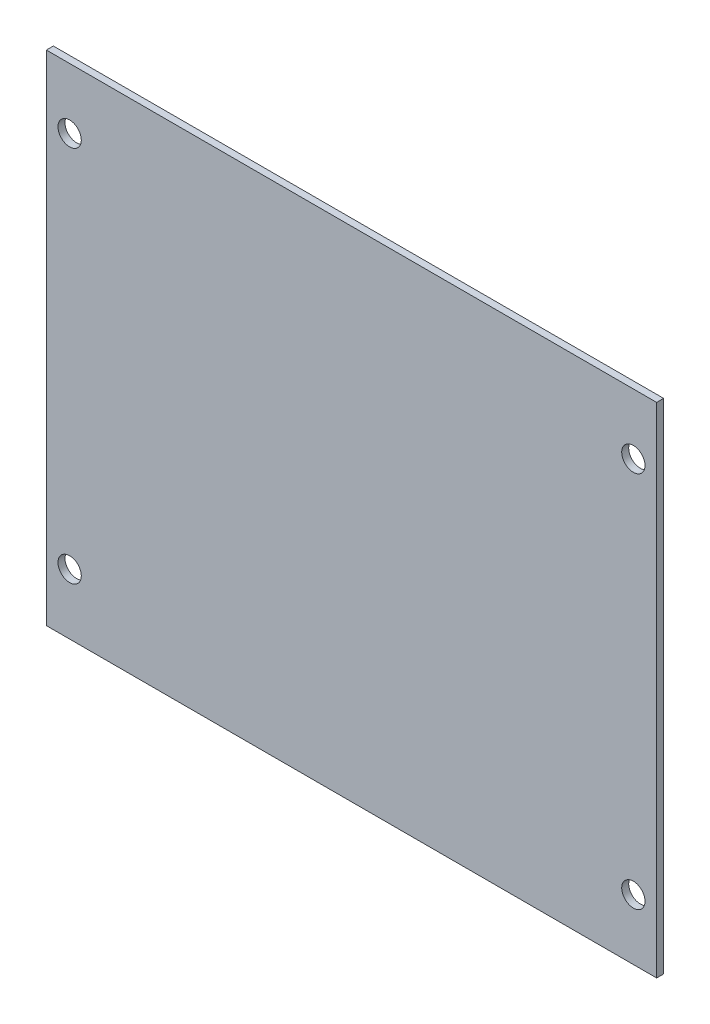
SolidWorks part; units mm, degrees
ref_plane "Alzado" through (0, 0, 0) normal (0, 0, 1) x (1, 0, 0)
ref_plane "Planta" through (0, 0, 0) normal (0, 1, 0) x (1, 0, 0)
ref_plane "Vista lateral" through (0, 0, 0) normal (1, 0, 0) x (0, 0, -1)
sketch "Croquis1" plane through (0, 0, 0) normal (0, 0, 1) x (1, 0, 0)
  line L1 (-55.0355, 36.5593) -> (75.9645, 36.5593)
  line L2 (-55.0355, 36.5593) -> (-55.0355, -70.4407)
  line L3 (-55.0355, -70.4407) -> (75.9645, -70.4407)
  line L4 (75.9645, 36.5593) -> (75.9645, -70.4407)
  dimension "D1" = 131
  dimension "D2" = 107
extrude "Saliente-Extruir1" add sketch "Croquis1" along normal blind 1.5
sketch "Croquis2" plane through (0, 0, 1.5) normal (0, 0, 1) x (1, 0, 0)
  line L0 (75.9645, -70.4407) -> (75.9645, 36.5593) construction
  line L1 (75.9645, 36.5593) -> (-55.0355, 36.5593) construction
  line L2 (-55.0355, 36.5593) -> (-55.0355, -70.4407) construction
  line L3 (-55.0355, -70.4407) -> (75.9645, -70.4407) construction
  circle A0 centre (-50.0355, 23.5593) radius 2.5
  circle A1 centre (70.9645, 23.5593) radius 2.5
  circle A2 centre (70.9645, -57.4407) radius 2.5
  circle A3 centre (-50.0355, -57.4407) radius 2.5
  dimension "D1" = 5
  dimension "D5" = 5
  dimension "D6" = 5
  dimension "D8" = 5
  dimension "D2" = 13
  dimension "D3" = 5
  dimension "D4" = 5
  dimension "D7" = 13
  dimension "D9" = 13
  dimension "D10" = 5
  dimension "D11" = 5
  dimension "D12" = 13
extrude "Cortar-Extruir1" cut sketch "Croquis2" against normal up to next
